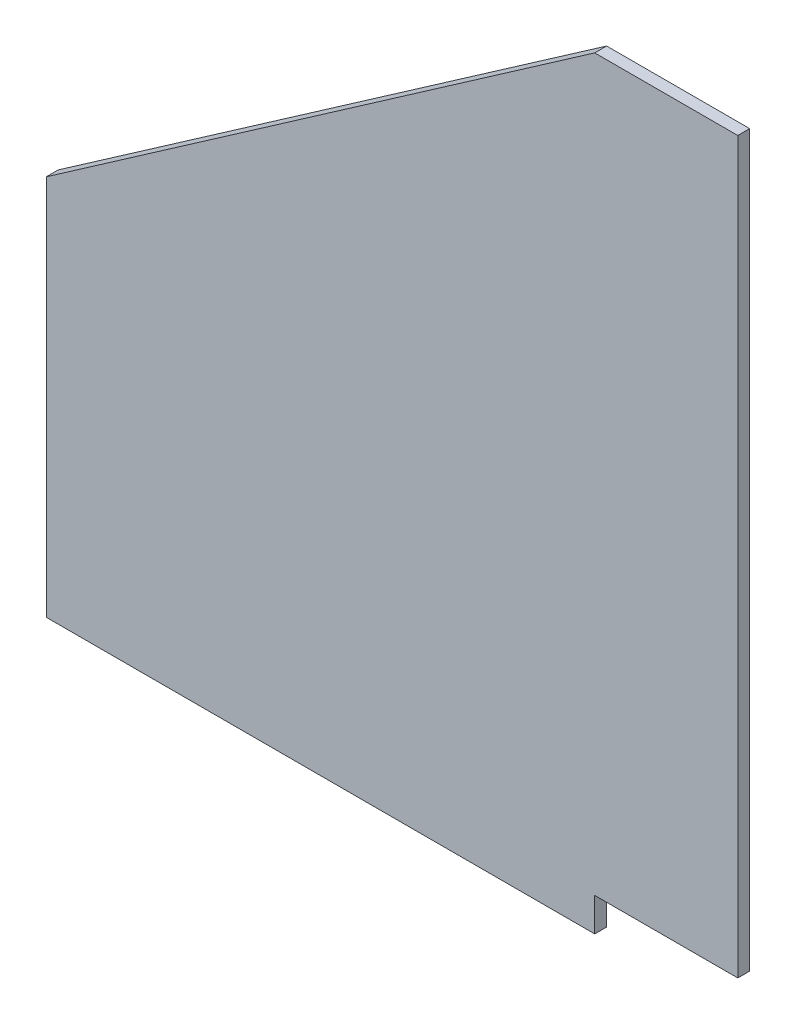
SolidWorks part; units mm, degrees
material "A-Glass Fiber"
ref_plane "Front Plane" through (0, 0, 0) normal (0, 0, 1) x (1, 0, 0)
ref_plane "Top Plane" through (0, 0, 0) normal (0, 1, 0) x (1, 0, 0)
ref_plane "Right Plane" through (0, 0, 0) normal (1, 0, 0) x (0, 0, -1)
sketch "Sketch1" plane through (0, 0, 0) normal (0, 0, 1) x (1, 0, 0)
  line L0 (0, 0) -> (0, 194.31)
  line L1 (0, 194.31) -> (-38.1, 194.31)
  line L3 (-184.15, -8.89) -> (-38.1, -8.89)
  line L4 (-38.1, -8.89) -> (-38.1, 0)
  line L5 (-38.1, 0) -> (0, 0)
  line L6 (-184.15, -8.89) -> (-184.15, 92.71)
  line L7 (-184.15, 92.71) -> (-38.1, 194.31)
  dimension "D1" = 194.31
  dimension "D2" = 146.05
  dimension "D3" = 38.1
  dimension "D4" = 203.2
  dimension "D5" = 38.1
  dimension "D6" = 101.6
extrude "Boss-Extrude1" add sketch "Sketch1" along normal blind 3.175
